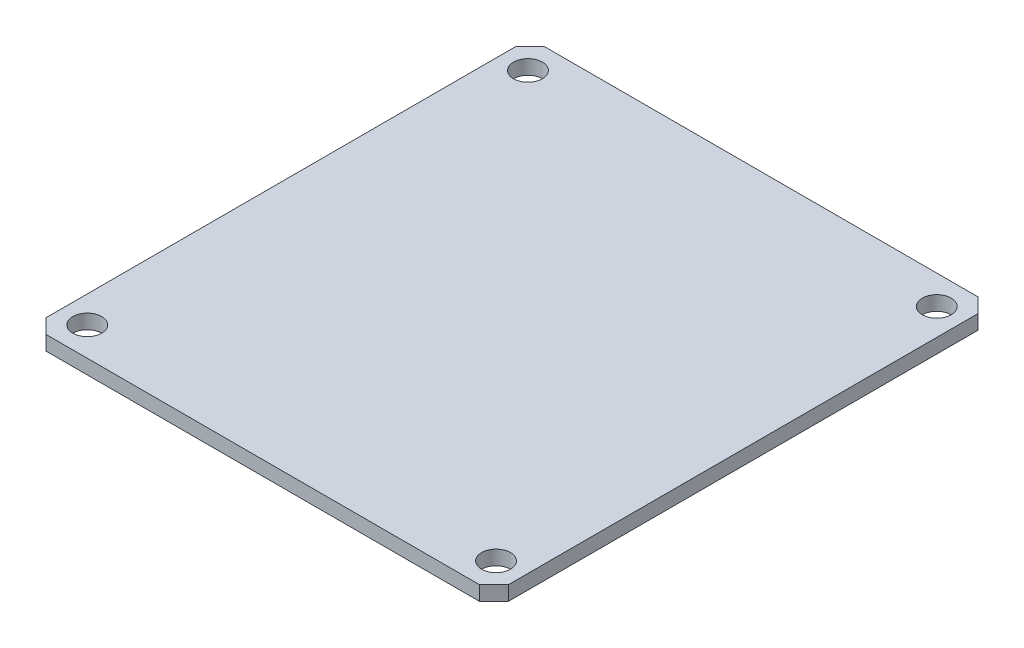
SolidWorks part; units mm, degrees
material "Epoxy, Unfilled"
ref_plane "Front Plane" through (0, 0, 0) normal (0, 0, 1) x (1, 0, 0)
ref_plane "Top Plane" through (0, 0, 0) normal (0, 1, 0) x (1, 0, 0)
ref_plane "Right Plane" through (0, 0, 0) normal (1, 0, 0) x (0, 0, -1)
sketch "Sketch1" plane through (0, 0, 0) normal (0, 1, 0) x (1, 0, 0)
  line L0 (-32, 32.5003) -> (-30.0003, 34.5)
  line L1 (-30, -34.5) -> (30, -34.5)
  line L2 (-32, -32.5) -> (-32, 32.5003)
  line L3 (-30.0003, 34.5) -> (30, 34.5)
  line L4 (32, -32.5) -> (32, 32.5)
  line L5 (-32, -34.5) -> (32, 34.5) construction
  line L6 (-32, 34.5) -> (32, -34.5) construction
  line L7 (30, 34.5) -> (32, 32.5)
  line L8 (-32, -32.5) -> (-30, -34.5)
  line L9 (30, -34.5) -> (32, -32.5)
  line L10 (-32, 34.5) -> (-32, 32.5003) construction
  line L11 (-32, 34.5) -> (-30.0003, 34.5) construction
  line L12 (30, 34.5) -> (32, 34.5) construction
  line L13 (32, 34.5) -> (32, 32.5) construction
  line L14 (-32, -32.5) -> (-32, -34.5) construction
  line L15 (-32, -34.5) -> (-30, -34.5) construction
  line L16 (32, -32.5) -> (32, -34.5) construction
  line L17 (32, -34.5) -> (30, -34.5) construction
  line L18 (-0.0002, 34.5) -> (0, -34.5) construction
  line L19 (-32, 0.0002) -> (32, 0) construction
  circle A0 centre (-28.2899, 30.5) radius 2
  circle A1 centre (28.2896, 30.5001) radius 2
  circle A2 centre (-28.29, -30.4997) radius 2
  circle A3 centre (28.2894, -30.5001) radius 2
  point P0 (0, 0)
  dimension "D11" = 4
  dimension "D12" = 4
  dimension "D1" = 64
  dimension "D2" = 69
  dimension "D3" = 2.828
  dimension "D5" = 2
  dimension "D9" = 2
  dimension "D7" = 2
  dimension "D4" = 1.9997
  dimension "D6" = 2
  dimension "D8" = 2
  dimension "D10" = 2
extrude "Boss-Extrude1" add sketch "Sketch1" along normal blind 2
